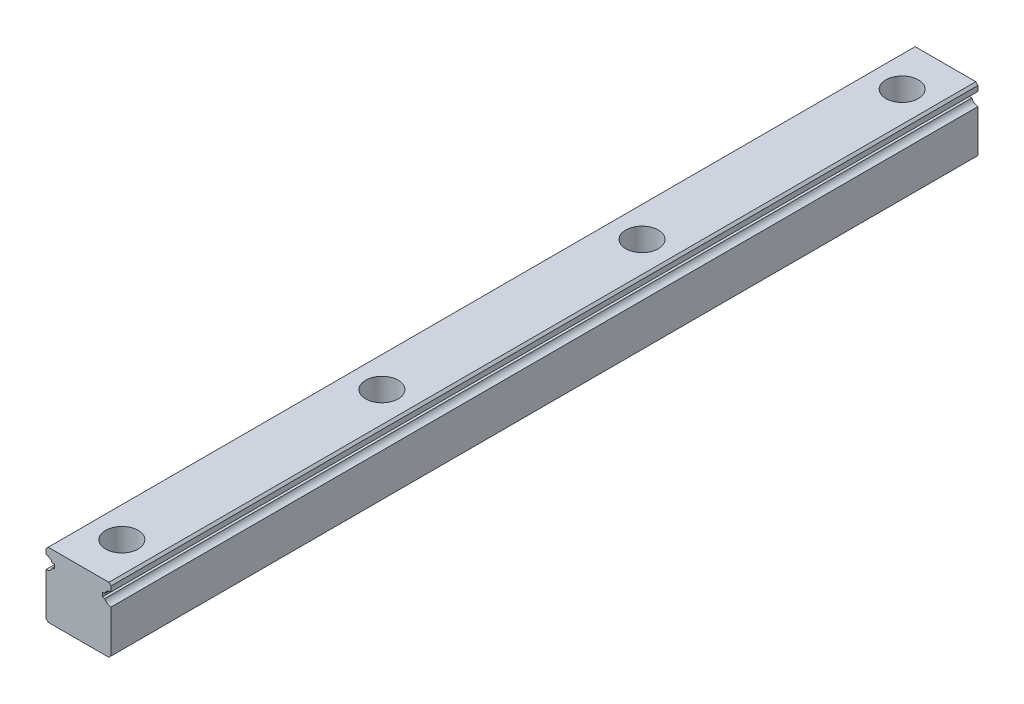
SolidWorks part; units mm, degrees
ref_plane "Front Plane" through (0, 0, 0) normal (0, 0, 1) x (1, 0, 0)
ref_plane "Top Plane" through (0, 0, 0) normal (0, 1, 0) x (1, 0, 0)
ref_plane "Right Plane" through (0, 0, 0) normal (1, 0, 0) x (0, 0, -1)
sketch "Sketch1" plane through (0, 0, 0) normal (0, 0, 1) x (1, 0, 0)
  line L0 (0, 0) -> (0, 21.7039) construction
  line L1 (7.5, 0) -> (-7.5, 0)
  line L2 (-7.5, 0) -> (-7.5, 11.3)
  line L3 (-7.5, 11.3) -> (-5.5, 11.3)
  line L4 (-5.5, 11.3) -> (-5.5, 12.3)
  line L5 (-5.5, 12.3) -> (-7.5, 12.3)
  line L6 (-7.5, 12.3) -> (-7.5, 15)
  line L7 (-7.5, 15) -> (7.5, 15)
  line L8 (7.5, 12.3) -> (7.5, 15)
  line L9 (5.5, 12.3) -> (7.5, 12.3)
  line L10 (5.5, 11.3) -> (5.5, 12.3)
  line L11 (7.5, 11.3) -> (5.5, 11.3)
  line L12 (7.5, 0) -> (7.5, 11.3)
  point P13 (0, 15)
  dimension "D1" = 7.5
  dimension "D2" = 15
  dimension "D3" = 1
  dimension "D4" = 11.3
  dimension "D5" = 2
  dimension "D6" = 2
extrude "Boss-Extrude1" add sketch "Sketch1" along normal blind 200
sketch "Sketch2" plane through (0, 0, 200) normal (0, 0, 1) x (1, 0, 0)
  line L0 (0, 0) -> (0, 15) construction
  line L1 (7.5, 15) -> (-7.5, 15) construction
  line L2 (-7.5, 11.8) -> (7.48, 11.8) construction
  line L3 (-5.5, 11.3) -> (-7.5, 11.3) construction
  circle A0 centre (-7.5, 11.8) radius 1.5
  circle A1 centre (7.5, 11.8) radius 1.5
  dimension "D2" = 3
  dimension "D1" = 0.5
extrude "Cut-Extrude1" cut sketch "Sketch2" against normal up to next
chamfer "Chamfer1" distance 0.5 angle 45 2 edges at (-7.5, 15, 100) (7.5, 15, 100)
chamfer "Chamfer2" distance 0.5 angle 45 2 edges at (-7.5, 0, 100) (7.5, 0, 100)
sketch "Sketch3" plane through (0, 15, 0) normal (0, 1, 0) x (1, 0, 0)
  line L0 (0, 0) -> (0, -200) construction
  line L1 (7, -200) -> (-7, -200) construction
  circle A0 centre (0, -190) radius 6.2393
  dimension "D1" = 10
hole_wizard "CBORE for M4 Hex Socket Head Cap Screw1" positions "3DSketch1" profile "Sketch4" counterbore size "M4" standard "ISO" end condition through all
sketch3d "3DSketch1"
  point P0 (0, 15, 190)
sketch "Sketch4" plane through (0, 15, 190) normal (1, 0, 0) x (0, 0, 1)
  line L0 (0, 0) -> (0, 15)
  line L1 (0, 15) -> (2.25, 15)
  line L3 (2.25, 15) -> (2.25, 5.3)
  line L4 (2.25, 5.3) -> (3.75, 5.3)
  line L5 (3.75, 5.3) -> (3.75, 0)
  line L7 (3.75, 0) -> (0, 0)
  line L11 (0, -6.35) -> (0, 107.95) construction
  dimension "Thru Hole Dia." = 4.5
  dimension "Thru Hole Depth" = 15
  dimension "C'Bore Dia." = 7.5
  dimension "C'Bore Depth" = 5.3
pattern_linear "LPattern1" count 4 spacing 60 along (0, 0, -1) of "CBORE for M4 Hex Socket Head Cap Screw1"
